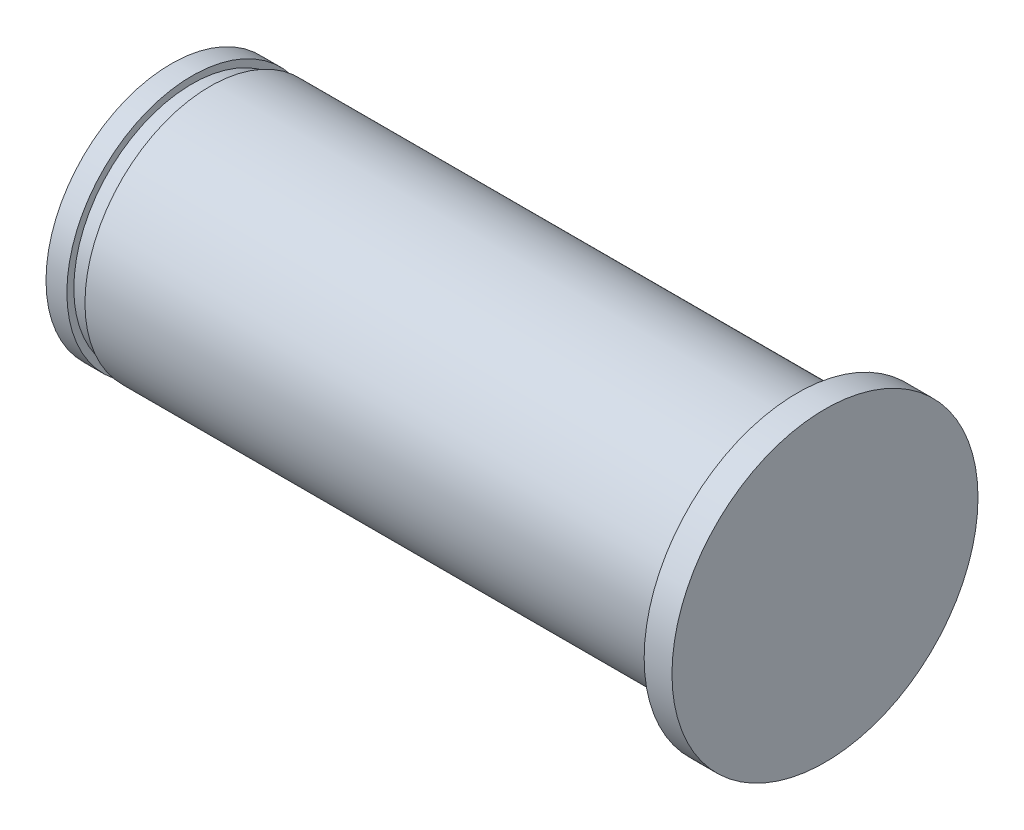
SolidWorks part; units mm, degrees
ref_plane "Přední rovina" through (0, 0, 0) normal (0, 0, 1) x (1, 0, 0)
ref_plane "Horní rovina" through (0, 0, 0) normal (0, 1, 0) x (1, 0, 0)
ref_plane "Pravá rovina" through (0, 0, 0) normal (1, 0, 0) x (0, 0, -1)
sketch "Skica1" plane through (0, 0, 0) normal (0, 0, 1) x (1, 0, 0)
  line L0 (-20.4031, 0) -> (29.0061, 0) construction
  line L1 (0, 0) -> (0, 9)
  line L2 (0, 9) -> (1.5, 9)
  line L3 (1.5, 9) -> (1.5, 8.5)
  line L4 (1.5, 8.5) -> (2.8, 8.5)
  line L5 (2.8, 8.5) -> (2.8, 9)
  line L6 (2.8, 9) -> (45, 9)
  line L7 (45, 9) -> (45, 11)
  line L8 (45, 11) -> (47, 11)
  line L9 (47, 11) -> (47, 0)
  line L10 (47, 0) -> (0, 0)
  point P13 (46, 11)
  dimension "D1" = 42.2
  dimension "D2" = 18
  dimension "D3" = 2
  dimension "D4" = 2
  dimension "D5" = 1.3
  dimension "D6" = 1.5
  dimension "D7" = 17
revolve "Rotovat1" add sketch "Skica1" angle 360 about L0
